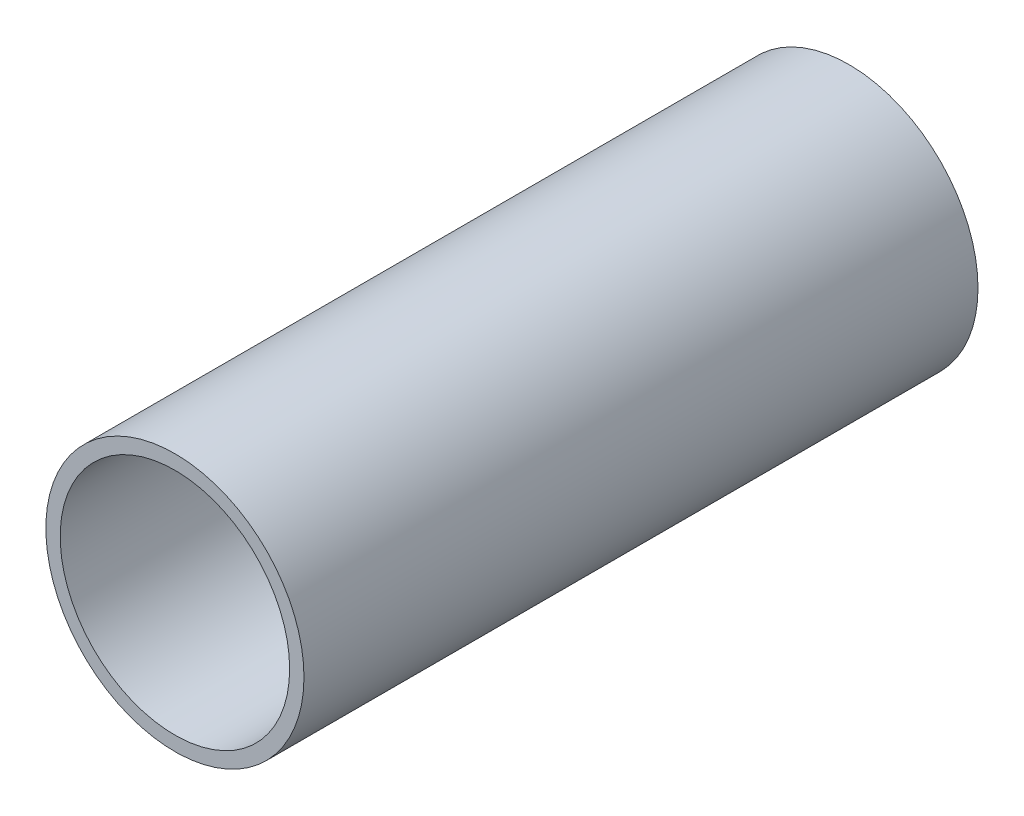
SolidWorks part; units mm, degrees
material "ABS PC"
ref_plane "Front Plane" through (0, 0, 0) normal (0, 0, 1) x (1, 0, 0)
ref_plane "Top Plane" through (0, 0, 0) normal (0, 1, 0) x (1, 0, 0)
ref_plane "Right Plane" through (0, 0, 0) normal (1, 0, 0) x (0, 0, -1)
sketch "Sketch1" plane through (0, 0, 0) normal (0, 0, 1) x (1, 0, 0)
  circle A0 centre (0, 0) radius 57.15
  circle A1 centre (0, 0) radius 50.8
  dimension "D1" = 114.3
  dimension "D2" = 101.6
extrude "Boss-Extrude1" add sketch "Sketch1" along normal mid plane 298.45
